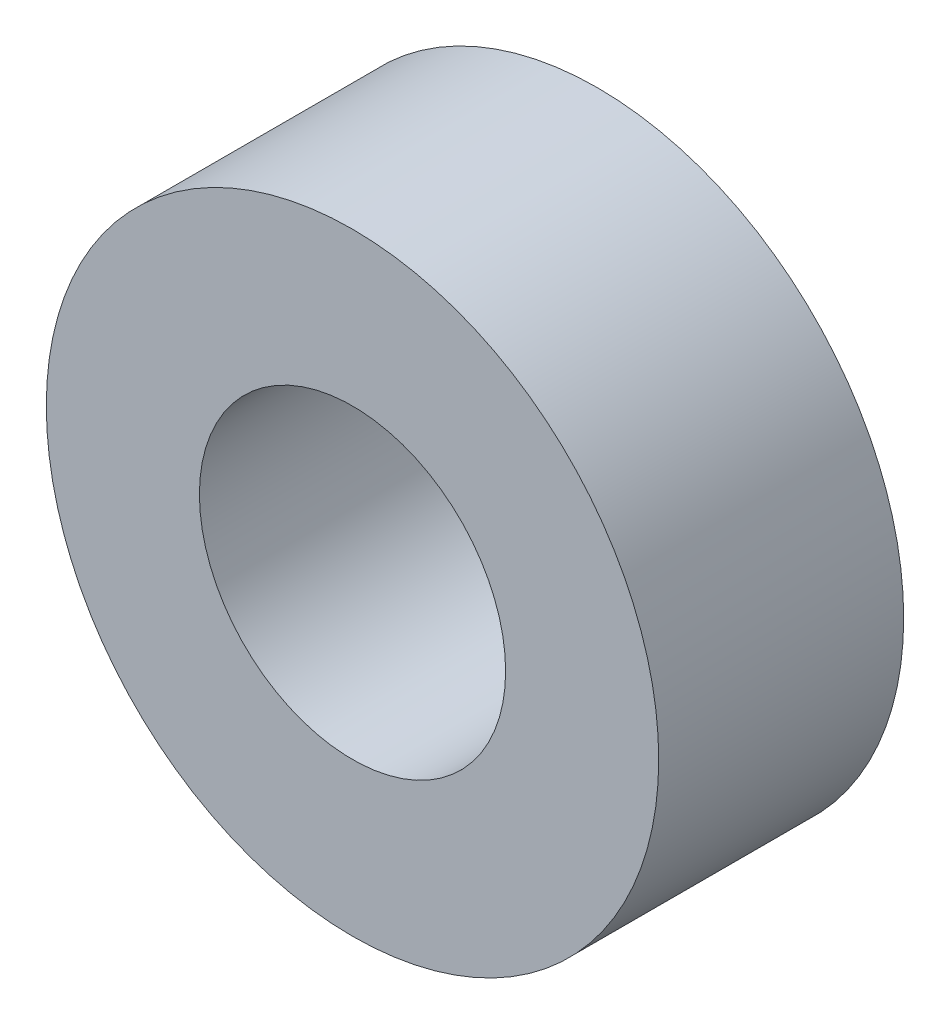
SolidWorks part; units mm, degrees
ref_plane "Front Plane" through (0, 0, 0) normal (0, 0, 1) x (1, 0, 0)
ref_plane "Top Plane" through (0, 0, 0) normal (0, 1, 0) x (1, 0, 0)
ref_plane "Right Plane" through (0, 0, 0) normal (1, 0, 0) x (0, 0, -1)
sketch "Sketch1" plane through (0, 0, 0) normal (0, 0, 1) x (1, 0, 0)
  circle A0 centre (0, 0) radius 5
  dimension "D1" = 10
extrude "Boss-Extrude1" add sketch "Sketch1" along normal blind 4
hole_wizard "Ø5.0mm Dowel Hole1" positions "Sketch3" profile "Sketch2" hole size "Ø5.0" standard "ISO"
sketch "Sketch3" plane through (0, 0, 0) normal (0, 0, -1) x (-1, 0, 0)
  point P0 (0, 0)
sketch "Sketch2" plane through (0, 0, 0) normal (1, 0, 0) x (0, 1, 0)
  line L0 (0, 0) -> (0, 14.2522)
  line L1 (0, 14.2522) -> (2.5, 12.75)
  line L2 (2.5, 12.75) -> (2.5, 0)
  line L5 (2.5, 0) -> (0, 0)
  line L10 (0, 14.2522) -> (-2.5, 12.75) construction
  line L11 (0, -6.35) -> (0, 107.95) construction
  dimension "Hole Dia." = 5
  dimension "Hole Depth" = 12.75
  dimension "Drill Angle" = 118
